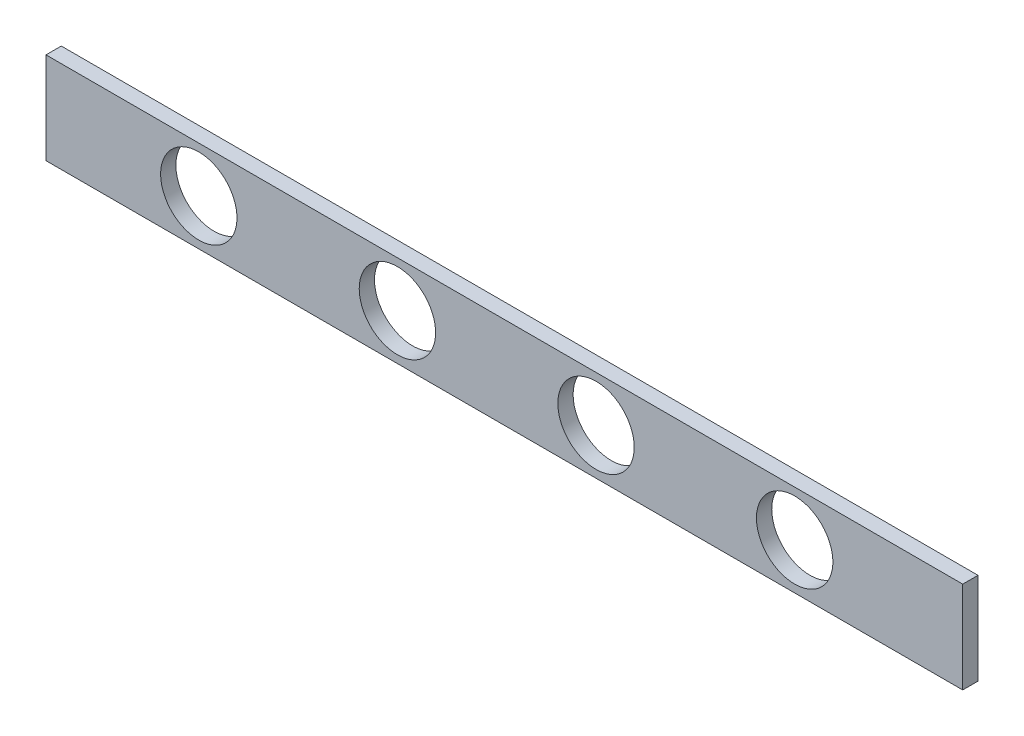
SolidWorks part; units mm, degrees
ref_plane "Front Plane" through (0, 0, 0) normal (0, 0, 1) x (1, 0, 0)
ref_plane "Top Plane" through (0, 0, 0) normal (0, 1, 0) x (1, 0, 0)
ref_plane "Right Plane" through (0, 0, 0) normal (1, 0, 0) x (0, 0, -1)
sketch "Sketch1" plane through (0, 0, 0) normal (0, 0, 1) x (1, 0, 0)
  line L1 (0, 0) -> (300, 0)
  line L2 (0, 0) -> (0, 30)
  line L3 (0, 30) -> (300, 30)
  line L4 (300, 0) -> (300, 30)
  dimension "D1" = 300
  dimension "D2" = 30
extrude "Boss-Extrude1" add sketch "Sketch1" along normal blind 5
sketch "Sketch2" plane through (0, 0, 0) normal (0, 0, -1) x (-1, 0, 0)
  line L0 (0, 30) -> (0, 0) construction
  circle A0 centre (-50, 15) radius 12.5
  circle A1 centre (-115, 15) radius 12.5
  circle A2 centre (-180, 15) radius 12.5
  circle A3 centre (-245, 15) radius 12.5
  point P4 (0, 15)
  dimension "D1" = 25
  dimension "D2" = 50
  dimension "D4" = 65
  dimension "D3" = 4
extrude "Cut-Extrude1" cut sketch "Sketch2" against normal through all
